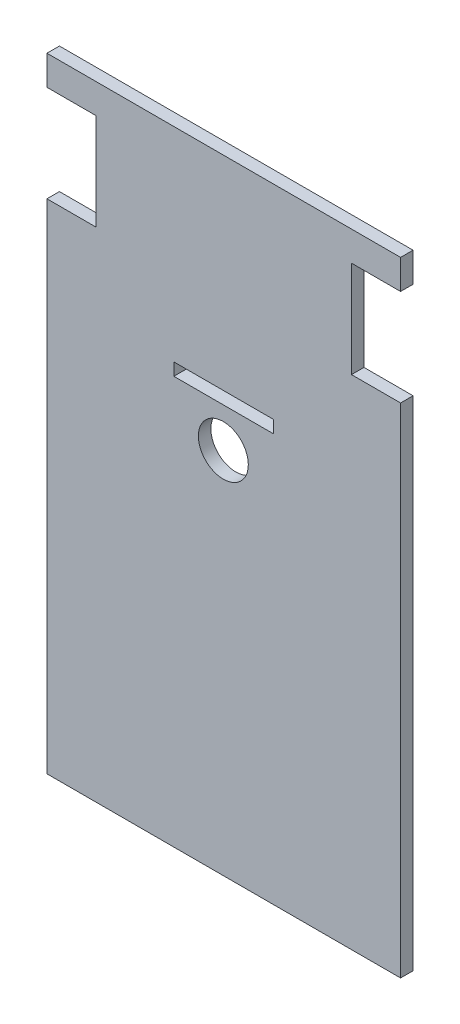
SolidWorks part; units mm, degrees
ref_plane "Alzado" through (0, 0, 0) normal (0, 0, 1) x (1, 0, 0)
ref_plane "Planta" through (0, 0, 0) normal (0, 1, 0) x (1, 0, 0)
ref_plane "Vista lateral" through (0, 0, 0) normal (1, 0, 0) x (0, 0, -1)
sketch "Model" plane through (0, 0, 0) normal (0, 0, 1) x (1, 0, 0)
  line L0 (16.403, 92.6003) -> (16.403, 85.5003)
  line L1 (101.403, 92.6003) -> (16.403, 92.6003)
  line L2 (101.403, 85.5003) -> (101.403, 92.6003)
  line L3 (89.603, 85.5003) -> (101.403, 85.5003)
  line L4 (89.603, 62.3003) -> (89.603, 85.5003)
  line L5 (101.403, 62.3003) -> (89.603, 62.3003)
  line L6 (101.403, -57.3997) -> (101.403, 62.3003)
  line L7 (16.403, -57.3997) -> (101.403, -57.3997)
  line L8 (16.403, 62.3003) -> (16.403, -57.3997)
  line L9 (16.403, 85.5003) -> (28.203, 85.5003)
  line L10 (28.203, 85.5003) -> (28.203, 62.3003)
  line L11 (28.203, 62.3003) -> (16.403, 62.3003)
  line L12 (70.903, 40.6003) -> (70.903, 43.6003)
  line L13 (70.903, 43.6003) -> (46.903, 43.6003)
  line L14 (46.903, 43.6003) -> (46.903, 40.6003)
  line L15 (46.903, 40.6003) -> (70.903, 40.6003)
  circle A0 centre (58.8023, 31.1299) radius 6
extrude "Saliente-Extruir1" add sketch "Model" along normal blind 3
